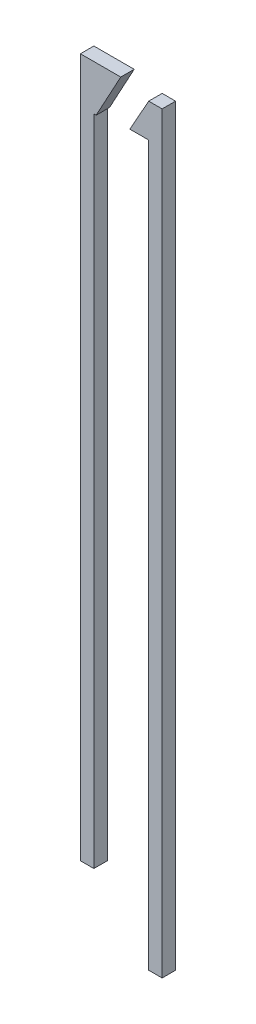
SolidWorks part; units mm, degrees
ref_plane "Front Plane" through (0, 0, 0) normal (0, 0, 1) x (1, 0, 0)
ref_plane "Top Plane" through (0, 0, 0) normal (0, 1, 0) x (1, 0, 0)
ref_plane "Right Plane" through (0, 0, 0) normal (1, 0, 0) x (0, 0, -1)
sketch "Sketch1" plane through (0, 0, 0) normal (0, 0, 1) x (1, 0, 0)
  line L0 (2.3917, 12.7826) -> (2.8917, 12.7826)
  line L1 (2.8917, 12.7826) -> (2.8917, -15.2174)
  line L2 (2.8917, -15.2174) -> (2.3917, -15.2174)
  line L3 (2.3917, -15.2174) -> (2.3917, 11.5288)
  line L4 (2.3917, 11.5288) -> (1.6917, 11.5288)
  line L5 (1.6917, 11.5288) -> (2.3917, 12.7826)
  line L6 (-0.1483, 13.0387) -> (1.3517, 13.0387)
  line L7 (-0.1483, 13.0387) -> (-0.1483, -12.9613)
  line L8 (-0.1483, -12.9613) -> (0.3517, -12.9613)
  line L9 (0.3517, -12.9613) -> (0.3517, 11.35)
  line L10 (0.3517, 11.35) -> (0.4351, 11.35)
  line L12 (0.4351, 11.35) -> (1.3517, 13.0387)
  point P5 (0, 0)
  point P11 (0.1017, -12.9613)
  point P14 (2.6417, -15.2174)
  dimension "D1" = 0.7
  dimension "D2" = 1.5
  dimension "D3" = 28
  dimension "D4" = 26
  dimension "D5" = 2.54
  dimension "D6" = 0.5
  dimension "D7" = 0.5
extrude "Boss-Extrude1" add sketch "Sketch1" along normal blind 0.5
